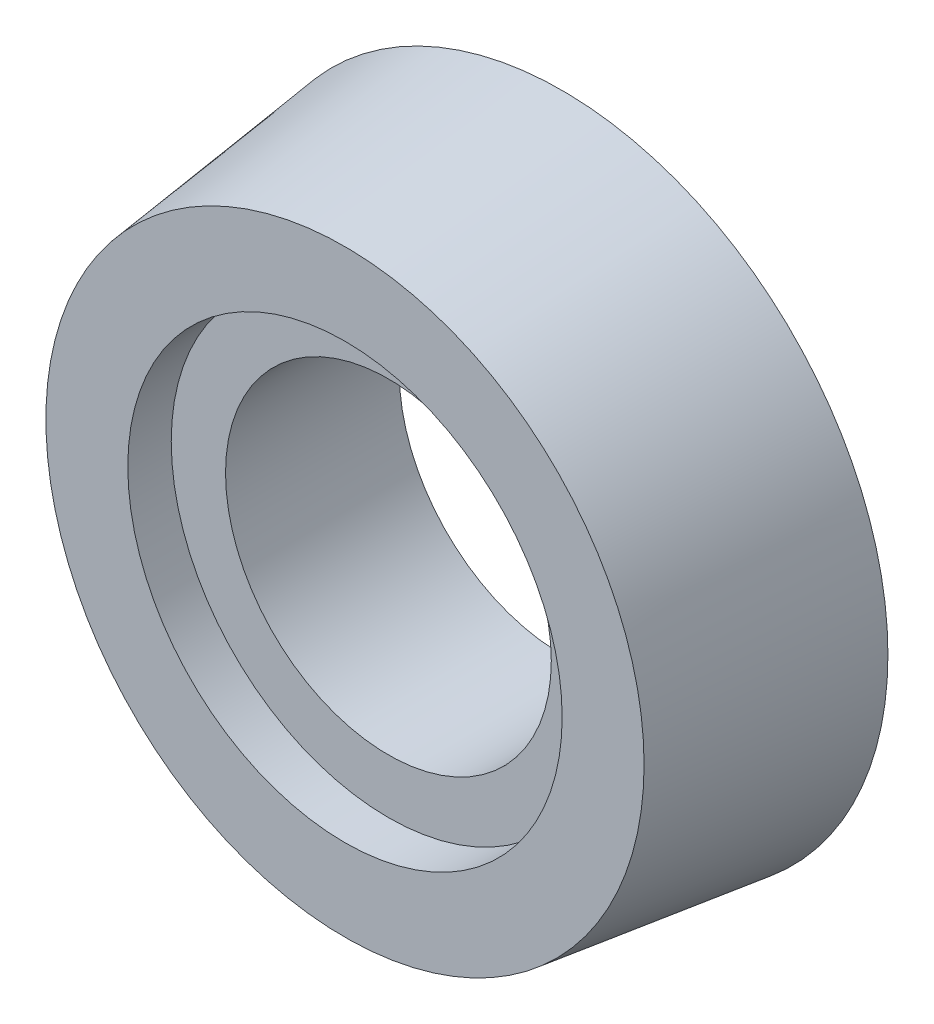
SolidWorks part; units mm, degrees
ref_plane "Front Plane" through (0, 0, 0) normal (0, 0, 1) x (1, 0, 0)
ref_plane "Top Plane" through (0, 0, 0) normal (0, 1, 0) x (1, 0, 0)
ref_plane "Right Plane" through (0, 0, 0) normal (1, 0, 0) x (0, 0, -1)
sketch "Sketch1" plane through (0, 0, 0) normal (0, 0, 1) x (1, 0, 0)
  line L0 (0, 0) -> (0, 36618.3769) construction
  line L1 (0, 0) -> (-36618.3769, 0) construction
  circle A0 centre (0, 0) radius 30
  dimension "D1" = 60
extrude "Boss-Extrude1" add sketch "Sketch1" along normal blind 20 draft 7
sketch "Sketch3" plane through (0, 0, 0) normal (0, 0, -1) x (-1, 0, 0)
  circle A0 centre (0, 0) radius 15
  dimension "D1" = 30
extrude "Cut-Extrude1" cut sketch "Sketch3" against normal through all
sketch "Sketch5" plane through (0, 0, 20) normal (0, 0, 1) x (1, 0, 0)
  circle A0 centre (0, 0) radius 20
  dimension "D1" = 40
extrude "Cut-Extrude2" cut sketch "Sketch5" against normal blind 4
